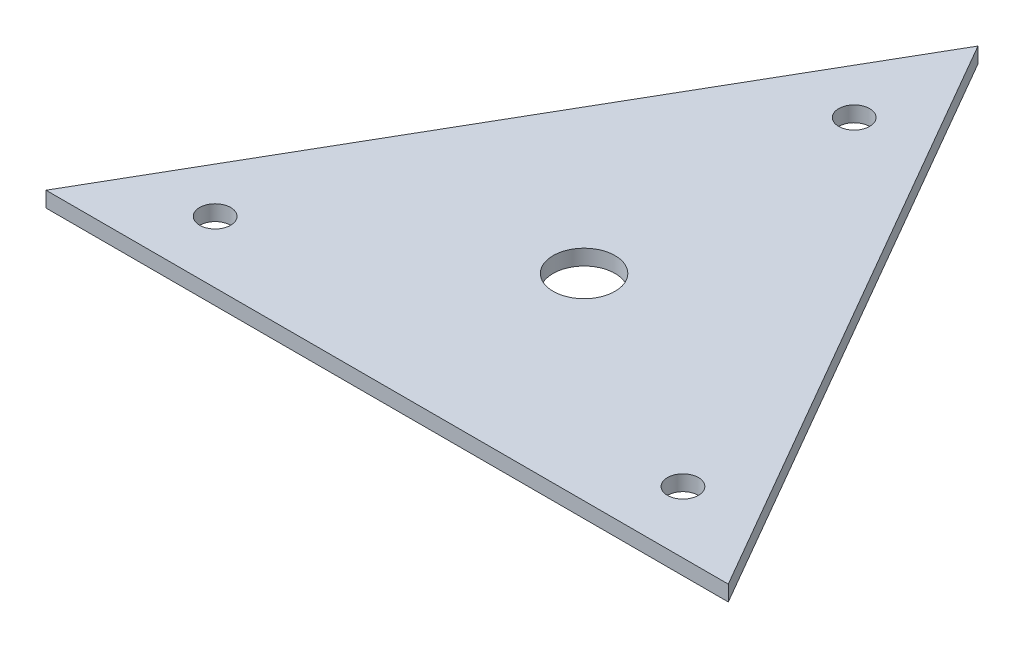
SolidWorks part; units mm, degrees
ref_plane "Front Plane" through (0, 0, 0) normal (0, 0, 1) x (1, 0, 0)
ref_plane "Top Plane" through (0, 0, 0) normal (0, 1, 0) x (1, 0, 0)
ref_plane "Right Plane" through (0, 0, 0) normal (1, 0, 0) x (0, 0, -1)
sketch "Sketch1" plane through (0, 0, 0) normal (0, 1, 0) x (1, 0, 0)
  line L0 (0, 0) -> (139.954, 0)
  line L1 (69.977, 121.2037) -> (139.954, 0)
  line L2 (69.977, 121.2037) -> (0, 0)
  line L3 (69.977, 40.4012) -> (69.977, 121.2037) construction
  line L4 (69.977, 40.4012) -> (0, 0) construction
  line L5 (69.977, 40.4012) -> (139.954, 0) construction
  circle A0 centre (69.977, 40.4012) radius 6.35
  circle A1 centre (117.957, 12.7) radius 3.175
  circle A2 centre (21.997, 12.7) radius 3.175
  circle A3 centre (69.977, 95.8037) radius 3.175
  dimension "D4" = 12.7
  dimension "D5" = 30
  dimension "D7" = 6.35
  dimension "D8" = 6.35
  dimension "D10" = 6.35
  dimension "D1" = 139.954
  dimension "D2" = 139.954
  dimension "D3" = 60
  dimension "D6" = 25.4
  dimension "D9" = 25.4
  dimension "D11" = 25.4
extrude "Boss-Extrude1" add sketch "Sketch1" along normal blind 3.175
